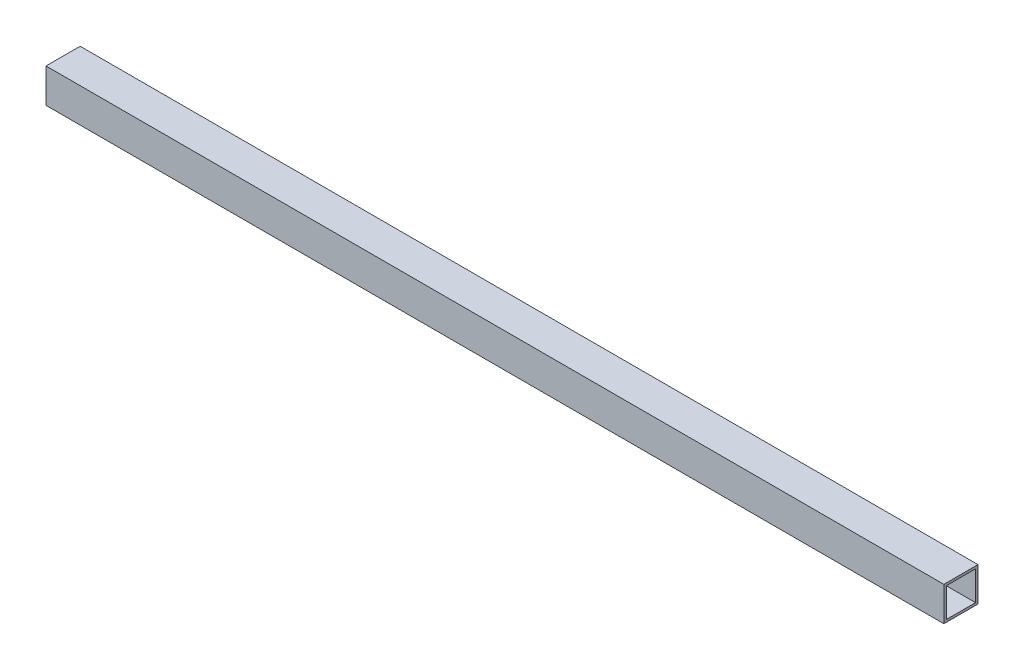
SolidWorks part; units mm, degrees
material "6061 Alloy"
ref_plane "Front Plane" through (0, 0, 0) normal (0, 0, 1) x (1, 0, 0)
ref_plane "Top Plane" through (0, 0, 0) normal (0, 1, 0) x (1, 0, 0)
ref_plane "Right Plane" through (0, 0, 0) normal (1, 0, 0) x (0, 0, -1)
sketch "Sketch1" plane through (0, 0, 0) normal (1, 0, 0) x (0, 0, -1)
  line L0 (41.275, 41.275) -> (3.175, 41.275)
  line L1 (0, 0) -> (44.45, 0)
  line L2 (44.45, 0) -> (44.45, 44.45)
  line L3 (44.45, 44.45) -> (0, 44.45)
  line L4 (0, 44.45) -> (0, 0)
  line L5 (3.175, 41.275) -> (3.175, 3.175)
  line L6 (3.175, 3.175) -> (41.275, 3.175)
  line L7 (41.275, 3.175) -> (41.275, 41.275)
  circle A0 centre (22.225, 22.225) radius 22.225 construction
  dimension "D1" = 44.45
  dimension "D2" = 3.175
extrude "Boss-Extrude1" add sketch "Sketch1" along normal mid plane 1168.4
